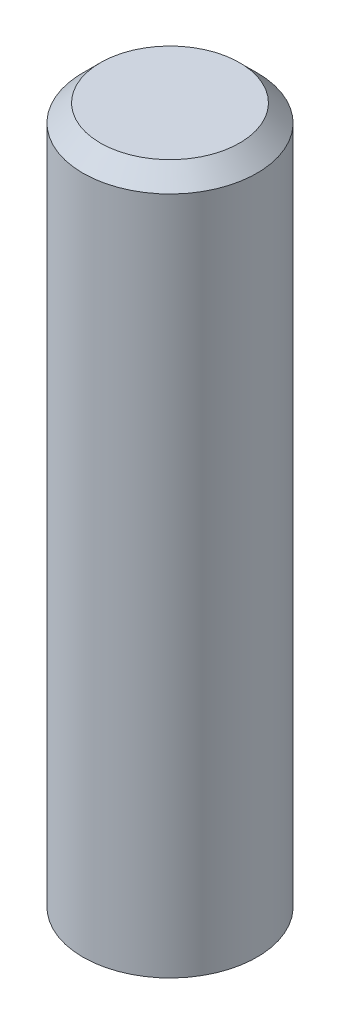
SolidWorks part; units mm, degrees
ref_plane "Piano frontale" through (0, 0, 0) normal (0, 0, 1) x (1, 0, 0)
ref_plane "Piano superiore" through (0, 0, 0) normal (0, 1, 0) x (1, 0, 0)
ref_plane "Piano destro" through (0, 0, 0) normal (1, 0, 0) x (0, 0, -1)
sketch "Schizzo1" plane through (0, 0, 0) normal (0, 1, 0) x (1, 0, 0)
  circle A0 centre (0, 0) radius 0.5
  dimension "D1" = 1
extrude "Estrusione-Estrusione1" add sketch "Schizzo1" along normal mid plane 4
chamfer "Smusso1" distance 0.1 angle 45 1 edges at (0, 2, 0.5)
